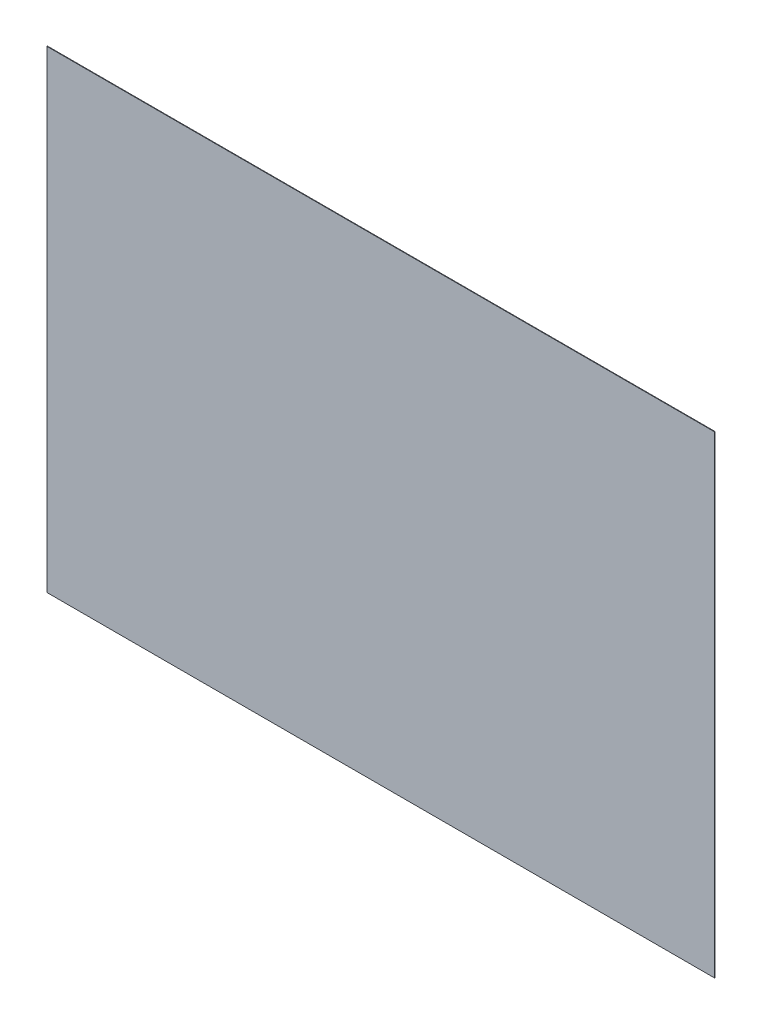
SolidWorks part; units mm, degrees
ref_plane "Front Plane" through (0, 0, 0) normal (0, 0, 1) x (1, 0, 0)
ref_plane "Top Plane" through (0, 0, 0) normal (0, 1, 0) x (1, 0, 0)
ref_plane "Right Plane" through (0, 0, 0) normal (1, 0, 0) x (0, 0, -1)
sketch "Sketch1" plane through (0, 0, 0) normal (0, 0, 1) x (1, 0, 0)
  line L1 (304.8, -215.9) -> (-304.8, -215.9)
  line L2 (304.8, -215.9) -> (304.8, 215.9)
  line L3 (304.8, 215.9) -> (-304.8, 215.9)
  line L4 (-304.8, -215.9) -> (-304.8, 215.9)
  line L5 (304.8, -215.9) -> (-304.8, 215.9) construction
  line L6 (304.8, 215.9) -> (-304.8, -215.9) construction
  point P0 (0, 0)
  dimension "D1" = 431.8
  dimension "D2" = 609.6
extrude "Boss-Extrude1" add sketch "Sketch1" along normal blind 0.5
sketch "Sketch2" plane through (0, 0, 0.5) normal (0, 0, 1) x (1, 0, 0)
  line L0 (-33.6333, 326.6) -> (1051.0334, 326.6) construction
